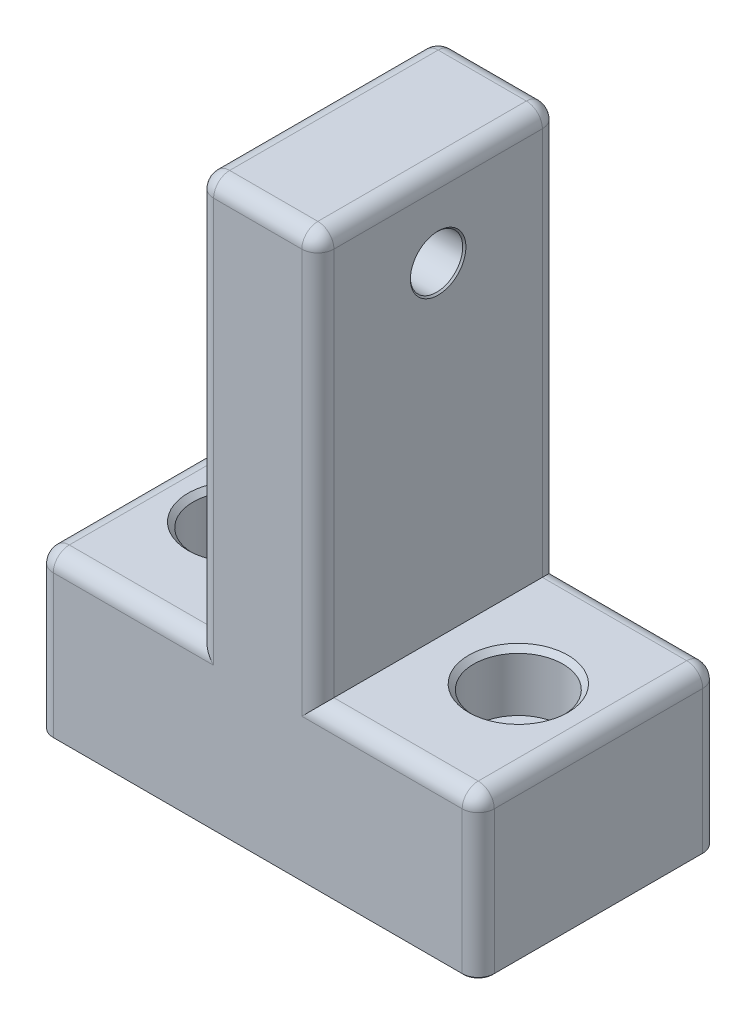
SolidWorks part; units mm, degrees
material "PE High Density"
ref_plane "Front Plane" through (0, 0, 0) normal (0, 0, 1) x (1, 0, 0)
ref_plane "Top Plane" through (0, 0, 0) normal (0, 1, 0) x (1, 0, 0)
ref_plane "Right Plane" through (0, 0, 0) normal (1, 0, 0) x (0, 0, -1)
sketch "Sketch1" plane through (0, 0, 0) normal (0, 0, 1) x (1, 0, 0)
  line L0 (0, 0) -> (0, 50.45)
  line L1 (0, 50.45) -> (-15, 50.45)
  line L2 (-15, 50.45) -> (-15, -20)
  line L3 (-15, -20) -> (20, -20)
  line L4 (20, -20) -> (20, 0)
  line L5 (20, 0) -> (0, 0)
  line L6 (-15, 40.45) -> (0, 40.45) construction
  line L7 (-15, -20) -> (-35, -20)
  line L8 (-35, -20) -> (-35, 0)
  line L9 (-35, 0) -> (-15, 0)
  dimension "D1" = 20
  dimension "D2" = 20
  dimension "D3" = 40.45
  dimension "D4" = 10
  dimension "D5" = 15
  dimension "D6" = 20
extrude "Boss-Extrude1" add sketch "Sketch1" along normal blind 30 contours L9 L8 L7 L2 | L6 L2 L3 L4 L5 L0 | L2 L6 L0 L1
sketch "Sketch2" plane through (0, 0, 0) normal (1, 0, 0) x (0, 0, -1)
  line L0 (0, 40.45) -> (-30, 40.45) construction
  line L1 (0, 50.45) -> (0, -20) construction
  line L3 (-30, 0) -> (-30, 50.45) construction
  circle A0 centre (-15, 40.45) radius 3.2639
  dimension "D1" = 6.5278
extrude "Cut-Extrude1" cut sketch "Sketch2" against normal through all
hole_wizard "CBORE for 1/4 Socket Head Cap Screw1" positions "Sketch4" profile "Sketch5" counterbore size "1/4" standard "ANSI Inch" end condition through all
sketch "Sketch4" plane through (0, 0, 0) normal (0, 1, 0) x (1, 0, 0)
  line L0 (-25, 0) -> (-25, -30) construction
  line L1 (-35, 0) -> (-15, 0) construction
  line L2 (-35, -30) -> (-15, -30) construction
  line L5 (10, -30) -> (10, 0) construction
  line L6 (20, -30) -> (0, -30) construction
  line L7 (20, 0) -> (0, 0) construction
  line L9 (-35, -30) -> (-35, 0) construction
  line L10 (20, -30) -> (20, 0) construction
  point P0 (-25, -15)
  point P2 (10, -15)
  point P23 (-25, -15)
  point P25 (10, -15)
  dimension "D1" = 10
  dimension "D2" = 10
sketch "Sketch5" plane through (-25, 0, 15) normal (1, 0, 0) x (0, 0, 1)
  line L0 (0, 0) -> (0, 20)
  line L1 (3.2639, 19.365) -> (3.8989, 20)
  line L2 (3.2639, 19.365) -> (3.2639, 7.985)
  line L3 (3.2639, 7.985) -> (3.8989, 7.35)
  line L4 (3.8989, 7.35) -> (5.5562, 7.35)
  line L5 (5.5562, 7.35) -> (5.5562, 0.635)
  line L6 (5.5562, 0.635) -> (6.1912, 0)
  line L7 (6.1912, 0) -> (0, 0)
  line L8 (-5.5562, 0.635) -> (-6.1912, 0) construction
  line L9 (-3.2639, 7.985) -> (-3.8989, 7.35) construction
  line L11 (0, -6.35) -> (0, 107.95) construction
  line L12 (3.8989, 20) -> (0, 20)
  line L13 (-3.2639, 19.365) -> (-3.8989, 20) construction
  dimension "Thru Hole Dia." = 6.5278
  dimension "Thru Hole Depth" = 20
  dimension "C'Bore Dia." = 11.1125
  dimension "C'Bore Depth" = 7.35
  dimension "Near C'Sink Dia." = 12.3825
  dimension "Near C'Sink Angle" = 90
  dimension "Mid C'Sink Dia." = 7.7978
  dimension "Mid C'Sink Angle" = 90
  dimension "Far C'Sink Dia." = 7.7978
  dimension "Far C'Sink Angle" = 90
sketch "Sketch7" plane through (0, -20, 0) normal (0, -1, 0) x (1, 0, 0)
  line L0 (-35, 15) -> (20, 15) construction
  line L1 (-35, 30) -> (-35, 0) construction
  line L2 (20, 30) -> (20, 0) construction
  line L4 (0, 18.25) -> (-15, 18.25)
  line L5 (0, 18.25) -> (0, 11.75)
  line L6 (0, 11.75) -> (-15, 11.75)
  line L7 (-15, 18.25) -> (-15, 11.75)
  line L8 (0, 18.25) -> (-15, 11.75) construction
  line L9 (0, 11.75) -> (-15, 18.25) construction
  point P6 (-7.5, 15)
  dimension "D1" = 6.5
  dimension "D2" = 15
extrude "Boss-Extrude2" add sketch "Sketch7" along normal blind 3 contours L5 L4 L7 L6
fillet "Fillet1" radius 2 22 edges at (-15, 50.45, 15) (-7.5, 50.45, 0) (0, 50.45, 15) (-7.5, 50.45, 30) (10, 0, 30) (20, 0, 15) (10, 0, 0) (-25, 0, 0) (-35, 0, 15) (-25, 0, 30) (0, 25.225, 0) (-15, 25.225, 0) (0, 25.225, 30) (-15, 25.225, 30) (20, -10, 30) (20, -10, 0) (-35, -10, 0) (-35, -10, 30) (0, -21.5, 11.75) (0, -21.5, 18.25) (-15, -21.5, 18.25) (-15, -21.5, 11.75)
chamfer "Chamfer1" distance 0.2 angle 45 18 edges at (-15, 43.7139, 15) (0, 40.45, 11.7361) (-7.5, -20, 0) (19.4142, -20, 0.5858) (-34.4142, -20, 0.5858) (20, -20, 15) (-35, -20, 15) (19.4142, -20, 29.4142) (-34.4142, -20, 29.4142) (-7.5, -20, 30) (-7.5, -23, 18.25) (-0.5858, -23, 17.6642) (-14.4142, -23, 17.6642) (0, -23, 15) (-15, -23, 15) (-0.5858, -23, 12.3358) (-14.4142, -23, 12.3358) (-7.5, -23, 11.75)
equation "\"screw_height\"= 40.45mm"
equation "\"D3@Sketch1\"=\"screw_height\""
